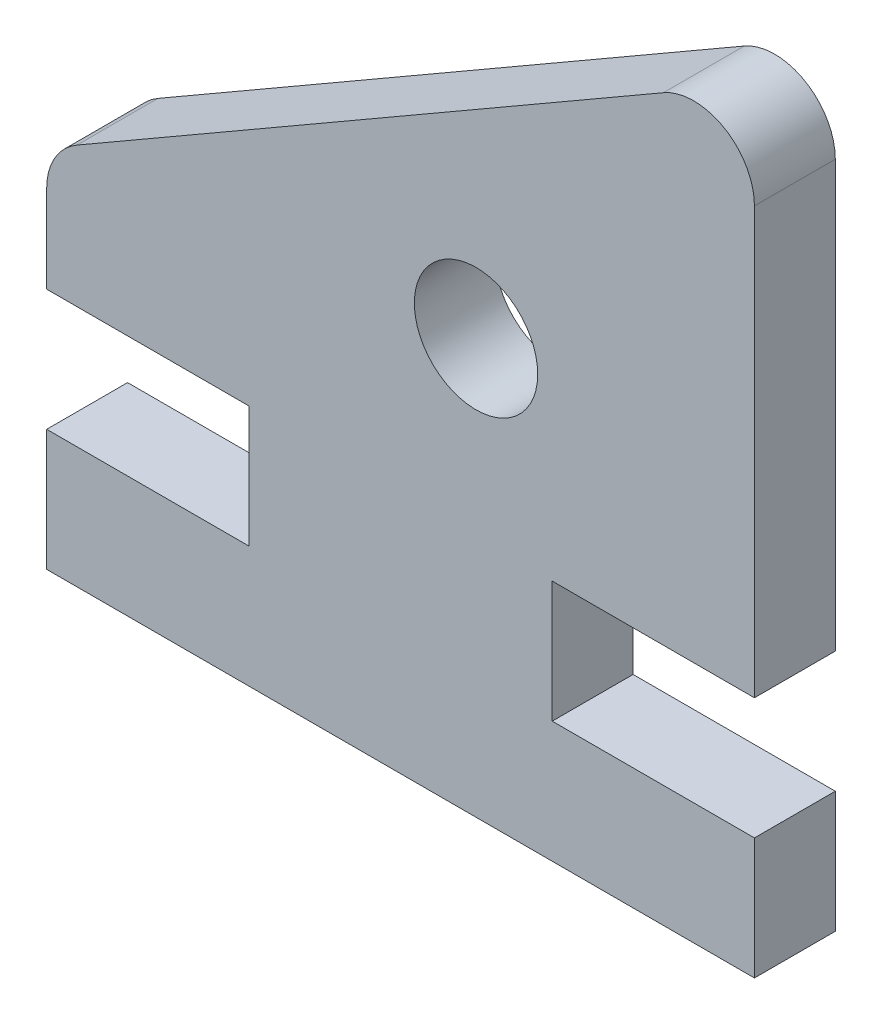
SolidWorks part; units mm, degrees
material "MDF"
ref_plane "Plano frontal" through (0, 0, 0) normal (0, 0, 1) x (1, 0, 0)
ref_plane "Plano superior" through (0, 0, 0) normal (0, 1, 0) x (1, 0, 0)
ref_plane "Plano direito" through (0, 0, 0) normal (1, 0, 0) x (0, 0, -1)
sketch "Esboço1" plane through (0, 0, 0) normal (0, 0, 1) x (1, 0, 0)
  line L0 (-35, 18.0566) -> (0, 38.2639)
  line L1 (0, 38.2639) -> (0, 0)
  line L2 (0, 0) -> (-35, 0)
  line L3 (-35, 0) -> (-35, 18.0566)
  line L5 (-25, 6) -> (-35, 6)
  line L6 (-25, 6) -> (-25, 12)
  line L7 (-25, 12) -> (-35, 12)
  line L8 (-35, 6) -> (-35, 12)
  line L9 (-25, 6) -> (-35, 12) construction
  line L10 (-25, 12) -> (-35, 6) construction
  line L11 (0, 6) -> (-10, 6)
  line L12 (0, 6) -> (0, 12)
  line L13 (0, 12) -> (-10, 12)
  line L14 (-10, 6) -> (-10, 12)
  line L15 (0, 6) -> (-10, 12) construction
  line L16 (0, 12) -> (-10, 6) construction
  circle A0 centre (-13.7679, 20.5) radius 3.05
  circle A1 centre (-13.7679, 20.5) radius 8.5 construction
  point P2 (-5, 9)
  point P8 (-30, 9)
  dimension "D10" = 6.1
  dimension "D11" = 17
  dimension "D1" = 30
  dimension "D2" = 18.0566
  dimension "D3" = 35
  dimension "D5" = 10
  dimension "D6" = 6
  dimension "D9" = 6
extrude "Ressalto-extrusão1" add sketch "Esboço1" along normal blind 4 contours L11 L14 L13 L1 L0 L3 L7 L6 L5 L2 A0
fillet "Filete1" radius 3 2 edges at (-35, 18.0566, 2) (0, 38.2639, 2)
